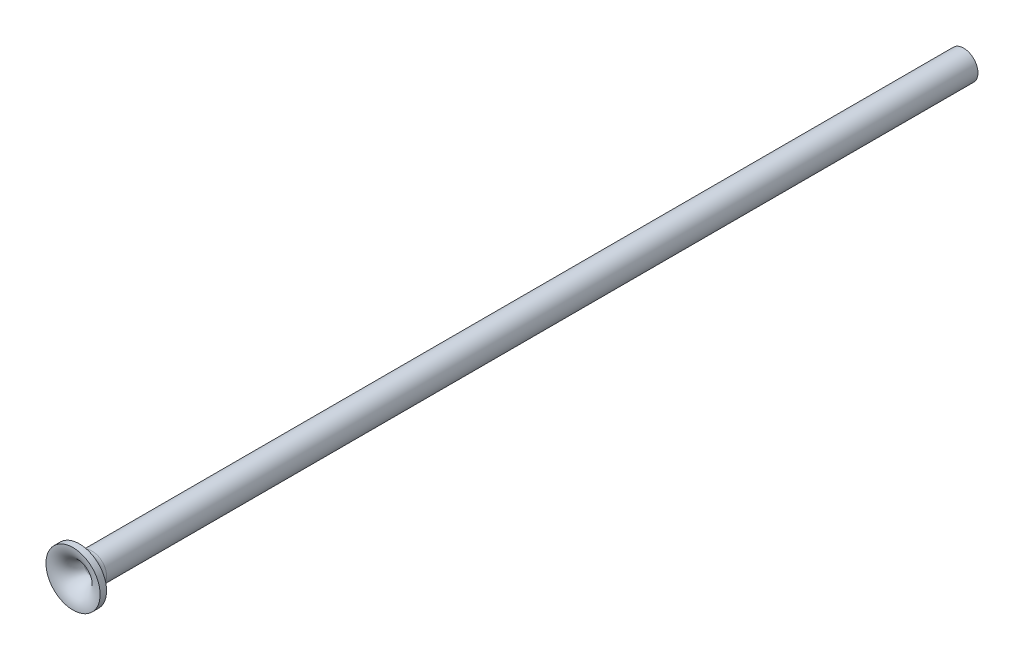
SolidWorks part; units mm, degrees
ref_plane "Front Plane" through (0, 0, 0) normal (0, 0, 1) x (1, 0, 0)
ref_plane "Top Plane" through (0, 0, 0) normal (0, 1, 0) x (1, 0, 0)
ref_plane "Right Plane" through (0, 0, 0) normal (1, 0, 0) x (0, 0, -1)
sketch "Sketch3" plane through (0, 0, 0) normal (0, 1, 0) x (1, 0, 0)
  line L0 (0, 0) -> (0, 4.7038) construction
  line L1 (0, 0) -> (-3, 0) construction
  line L2 (-3, -2.125) -> (-3, -1.4125)
  line L3 (-0.875, 0) -> (-0.875, 96.5)
  line L4 (-1.5875, 0) -> (-1.5875, 96.5)
  line L5 (-1.5875, 96.5) -> (-0.875, 96.5)
  arc A0 (-0.875, 0) -> (-3, -2.125) centre (-3, 0) cw
  arc A1 (-1.5875, 0) -> (-3, -1.4125) centre (-3, 0) cw
  dimension "D1" = 3
  dimension "D2" = 1.75
  dimension "D3" = 3.175
  dimension "D4" = 96.5
revolve "Revolve2" add sketch "Sketch3" angle 360 about L0
